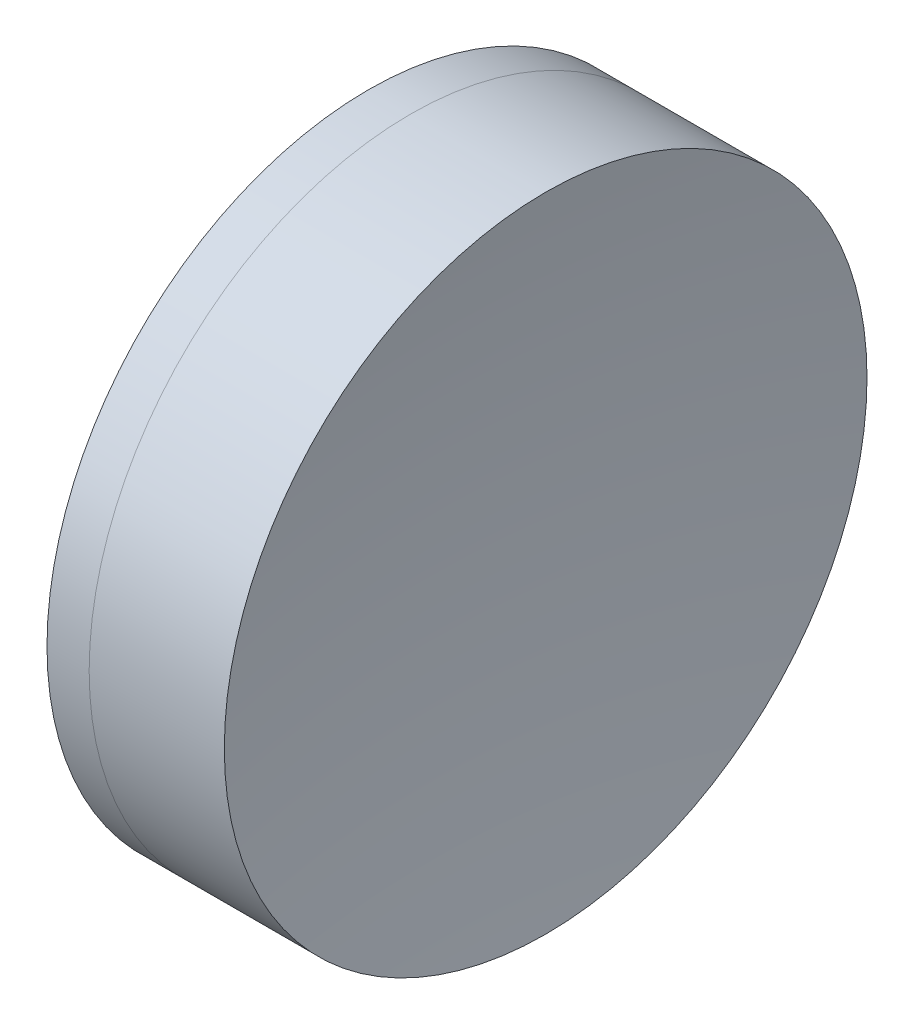
SolidWorks part; units mm, degrees
ref_plane "前视基准面" through (0, 0, 0) normal (0, 0, 1) x (1, 0, 0)
ref_plane "上视基准面" through (0, 0, 0) normal (0, 1, 0) x (1, 0, 0)
ref_plane "右视基准面" through (0, 0, 0) normal (1, 0, 0) x (0, 0, -1)
sketch "草图1" plane through (0, 0, 0) normal (0, 1, 0) x (1, 0, 0)
  line L0 (-0.8161, 0) -> (118.0272, 0) construction
  line L1 (98.4308, -15) -> (100.399, -15)
  line L2 (98.4308, 15) -> (100.399, 15)
  arc A0 (100.399, -15) -> (100.399, 15) centre (64.2149, 0) ccw
  arc A1 (98.4308, 15) -> (98.4308, -15) centre (128.3849, 0) ccw
  point P10 (94.8849, 0)
  point P11 (103.3849, 0)
  dimension "D3" = 33.5
  dimension "D4" = 39.17
  dimension "D1" = 15
  dimension "D2" = 15
  dimension "D5" = 8.5
revolve "旋转1" add sketch "草图1" angle 360 about L0
sketch "草图2" plane through (0, 0, 0) normal (0, 1, 0) x (1, 0, 0)
  line L0 (-0.5519, 0) -> (162.8134, 0) construction
  line L2 (100.399, 15) -> (106.7084, 15)
  line L3 (100.399, -15) -> (106.7084, -15)
  arc A0 (106.7084, 15) -> (106.7084, -15) centre (206.2749, 0) ccw
  arc A1 (100.399, -15) -> (100.399, 15) centre (64.2149, 0) ccw construction
  arc A2 (100.399, -15) -> (100.399, 15) centre (64.2149, 0) ccw
  point P4 (103.3849, 0)
  point P8 (105.5849, 0)
  dimension "D1" = 100.69
  dimension "D2" = 2.2
revolve "旋转2" add sketch "草图2" angle 360 about L0
